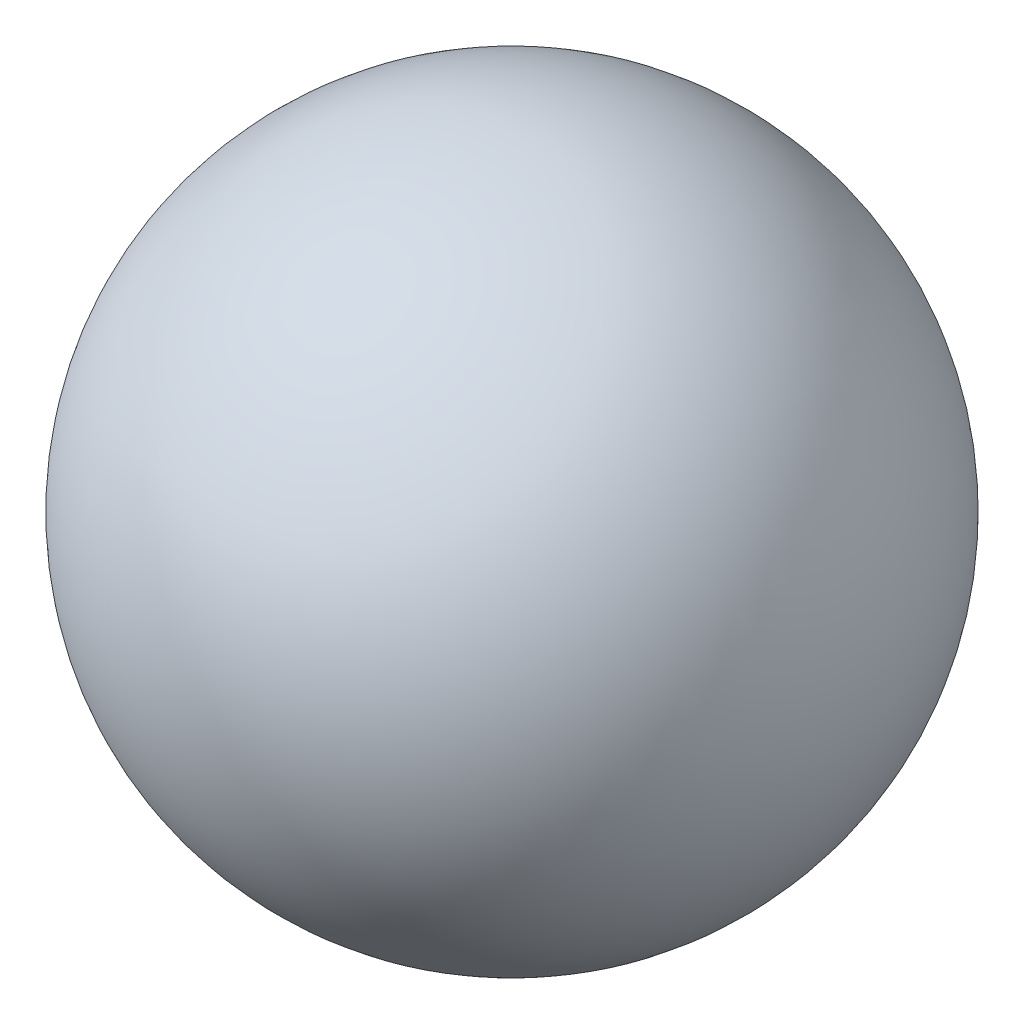
SolidWorks part; units mm, degrees
material "Silicon Rubber"
ref_plane "Front" through (0, 0, 0) normal (0, 0, 1) x (1, 0, 0)
ref_plane "Top" through (0, 0, 0) normal (0, 1, 0) x (1, 0, 0)
ref_plane "Right" through (0, 0, 0) normal (1, 0, 0) x (0, 0, -1)
sketch "Sketch1" plane through (0, 0, 0) normal (0, 0, 1) x (1, 0, 0)
  line L0 (0, 0) -> (0, 200) construction
  line L1 (0, 200) -> (0, 0)
  arc A0 (0, 200) -> (0, 0) centre (0, 100) cw
  dimension "D1" = 200
revolve "Revolve1" add sketch "Sketch1" angle 360 about L0
